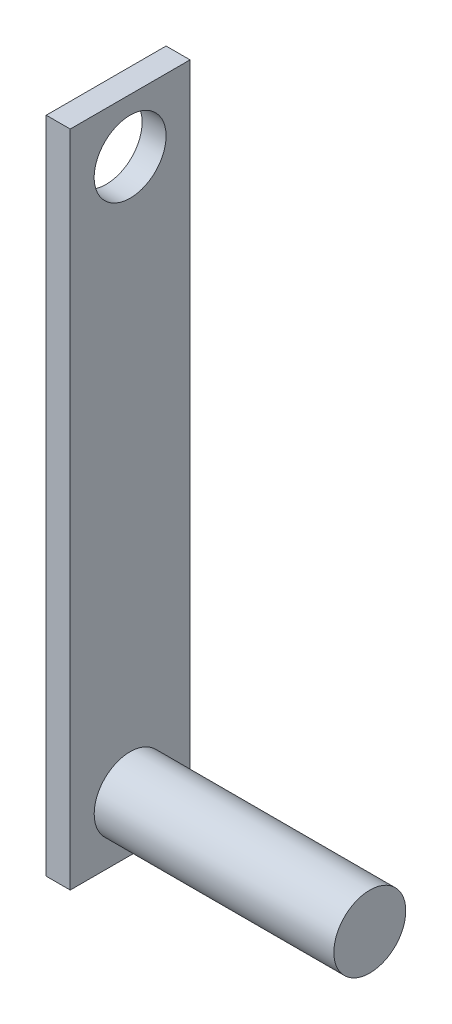
SolidWorks part; units mm, degrees
ref_plane "Front Plane" through (0, 0, 0) normal (0, 0, 1) x (1, 0, 0)
ref_plane "Top Plane" through (0, 0, 0) normal (0, 1, 0) x (1, 0, 0)
ref_plane "Right Plane" through (0, 0, 0) normal (1, 0, 0) x (0, 0, -1)
sketch "Sketch1" plane through (0, 0, 0) normal (1, 0, 0) x (0, 0, -1)
  line L1 (-5, -27.5) -> (5, -27.5)
  line L2 (-5, -27.5) -> (-5, 27.5)
  line L3 (-5, 27.5) -> (5, 27.5)
  line L4 (5, -27.5) -> (5, 27.5)
  line L5 (-5, -27.5) -> (5, 27.5) construction
  line L6 (-5, 27.5) -> (5, -27.5) construction
  point P0 (0, 0)
  dimension "D1" = 55
  dimension "D2" = 10
extrude "Boss-Extrude1" add sketch "Sketch1" along normal blind 2
sketch "Sketch2" plane through (2, 0, 0) normal (1, 0, 0) x (0, 0, -1)
  circle A0 centre (0, 23) radius 3
  dimension "D1" = 23
extrude "Cut-Extrude1" cut sketch "Sketch2" against normal up to surface (2 mm away) up to face at (0, 0, 0)
sketch "Sketch3" plane through (2, 0, 0) normal (1, 0, 0) x (0, 0, -1)
  circle A0 centre (0, -23) radius 3
  dimension "D1" = 23
extrude "Boss-Extrude2" add sketch "Sketch3" along normal blind 20
